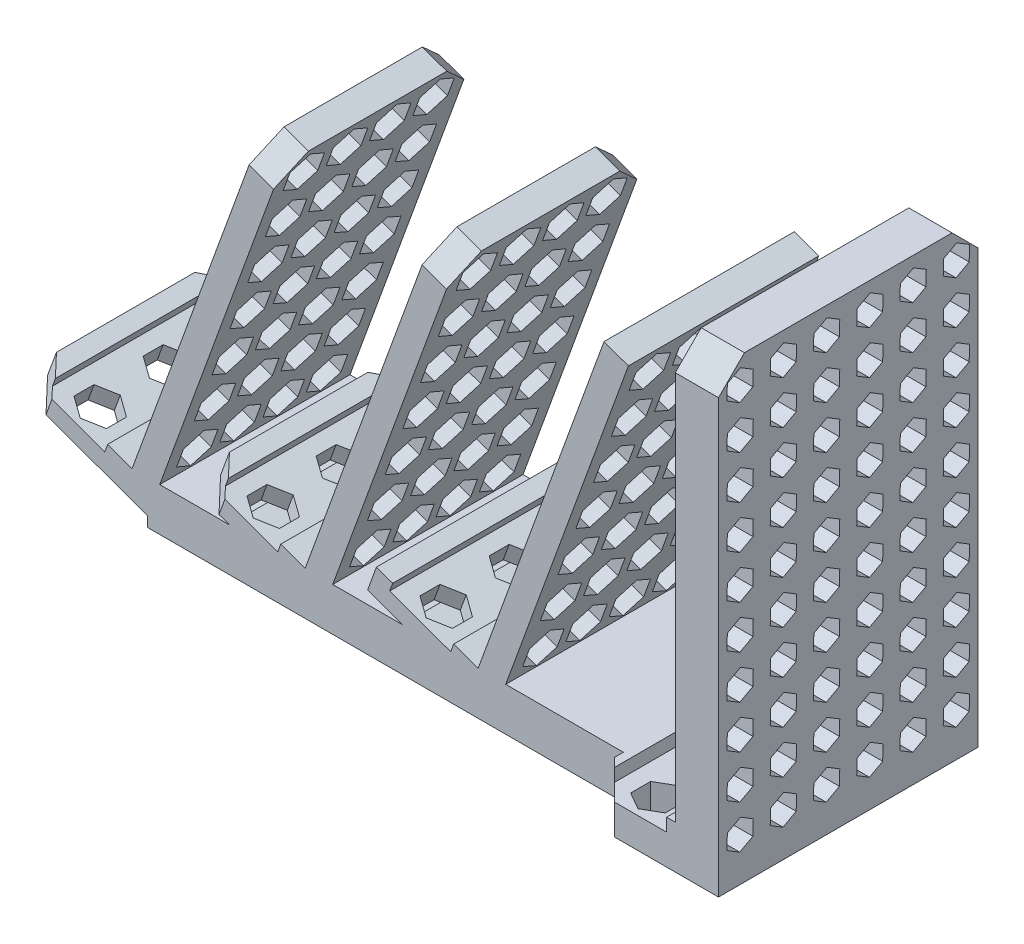
SolidWorks part; units mm, degrees
ref_plane "Front Plane" through (0, 0, 0) normal (0, 0, 1) x (1, 0, 0)
ref_plane "Top Plane" through (0, 0, 0) normal (0, 1, 0) x (1, 0, 0)
ref_plane "Right Plane" through (0, 0, 0) normal (1, 0, 0) x (0, 0, -1)
sketch "Sketch1" plane through (0, 0, 0) normal (0, 1, 0) x (1, 0, 0)
  line L1 (70, -22) -> (-70, -22)
  line L2 (70, -22) -> (70, 22)
  line L3 (70, 22) -> (-70, 22)
  line L4 (-70, -22) -> (-70, 22)
  line L5 (70, -22) -> (-70, 22) construction
  line L6 (70, 22) -> (-70, -22) construction
  point P0 (0, 0)
  dimension "D1" = 44
  dimension "D2" = 140
extrude "Boss-Extrude1" add sketch "Sketch1" along normal mid plane 10
sketch "Sketch2" plane through (0, 0, 0) normal (0, 0, 1) x (1, 0, 0)
  line L0 (-44.4684, 85) -> (-73.586, 5)
  line L1 (-70, -5) -> (70, -5) construction
  line L2 (-73.586, 5) -> (-97.0784, 13.5505)
  line L3 (-70, 5) -> (70, 5) construction
  line L4 (-38.8303, 82.9479) -> (-70, -2.6903)
  line L5 (-70, -2.6903) -> (-99.1305, 7.9123)
  line L6 (-99.1305, 7.9123) -> (-97.0784, 13.5505)
  line L7 (-44.4684, 85) -> (-38.8303, 82.9479)
  line L8 (-70, 5) -> (-70, -5) construction
  dimension "D1" = 20
  dimension "D2" = 25
  dimension "D3" = 80
  dimension "D4" = 6
  dimension "D5" = 0
extrude "Boss-Extrude2" add sketch "Sketch2" along normal mid plane 44
pattern_linear "LPattern1" count 3 spacing 40 along (1, 0, 0) of "Boss-Extrude2"
sketch "Sketch3" plane through (0, 5, 0) normal (0, 1, 0) x (1, 0, 0)
  line L5 (70, -22) -> (70, 22) construction
  line L6 (60, 30) -> (70, 30)
  line L7 (60, 30) -> (60, -30)
  line L8 (60, -30) -> (70, -30)
  line L9 (70, 30) -> (70, -30)
  line L10 (0, 0) -> (93.7204, 0) construction
  dimension "D1" = 30
  dimension "D2" = 60
  dimension "D3" = 10
extrude "Boss-Extrude3" add sketch "Sketch3" along normal blind 96 contours L9 L8 L7 L6
sketch "Sketch4" plane through (70, 0, 0) normal (1, 0, 0) x (0, 0, -1)
  line L0 (-22, -5) -> (22, -5) construction
  line L1 (-30, 5) -> (30, 5)
  line L2 (-30, 5) -> (-30, -5)
  line L3 (-30, -5) -> (30, -5)
  line L4 (30, 5) -> (30, -5)
  line L5 (30, 101) -> (30, 5) construction
extrude "Boss-Extrude4" add sketch "Sketch4" against normal blind 30
sketch "Sketch5" plane through (0, 0, 22) normal (0, 0, 1) x (1, 0, 0)
  line L0 (-93.3196, 12.1824) -> (-79.2242, 7.0521)
  line L1 (-73.586, 5) -> (-97.0784, 13.5505) construction
  line L2 (-79.2242, 7.0521) -> (-79.9082, 5.1727)
  line L3 (-79.9082, 5.1727) -> (-94.0036, 10.303)
  line L4 (-94.0036, 10.303) -> (-93.3196, 12.1824)
  line L5 (-44.4684, 85) -> (-73.586, 5) construction
  line L6 (-39.9082, 5.1727) -> (-54.0036, 10.303)
  line L7 (-53.3196, 12.1824) -> (-39.2242, 7.0521)
  line L8 (-54.0036, 10.303) -> (-53.3196, 12.1824)
  line L9 (-39.2242, 7.0521) -> (-39.9082, 5.1727)
  line L10 (0.0918, 5.1727) -> (-14.0036, 10.303)
  line L11 (-13.3196, 12.1824) -> (0.7758, 7.0521)
  line L12 (-14.0036, 10.303) -> (-13.3196, 12.1824)
  line L13 (0.7758, 7.0521) -> (0.0918, 5.1727)
  dimension "D1" = 90
  dimension "D2" = 2
  dimension "D3" = 15
  dimension "D4" = 6
  dimension "D5" = 3
extrude "Cut-Extrude1" cut sketch "Sketch5" against normal through all
sketch "Sketch6" plane through (0, 0, 30) normal (0, 0, 1) x (1, 0, 0)
  line L0 (40, 5) -> (60, 5) construction
  line L1 (42, 5) -> (58, 5)
  line L2 (42, 5) -> (42, 2)
  line L3 (42, 2) -> (58, 2)
  line L4 (58, 5) -> (58, 2)
  line L5 (40, 5) -> (40, -5) construction
  line L6 (60, 101) -> (60, 5) construction
  dimension "D1" = 2
  dimension "D2" = 2
  dimension "D3" = 3
extrude "Cut-Extrude2" cut sketch "Sketch6" against normal through all
sketch "Sketch7" plane through (-66.5851, 24.235, 0) normal (-0.9397, 0.342, 0) x (0, 0, 1)
  line L0 (-15, 64.6648) -> (-15, -20.4694) construction
  line L3 (22, 64.6648) -> (-22, 64.6648) construction
  line L10 (22, -20.4694) -> (-22, -20.4694) construction
  line L11 (-22, 64.6648) -> (-22, -20.4694) construction
  line L12 (-15, 63.2836) -> (-19, 60.9742)
  line L13 (-19, 60.9742) -> (-19, 56.3554)
  line L14 (-19, 56.3554) -> (-15, 54.046)
  line L15 (-15, 54.046) -> (-11, 56.3554)
  line L16 (-11, 56.3554) -> (-11, 60.9742)
  line L17 (-11, 60.9742) -> (-15, 63.2836)
  line L18 (-15, 51.2836) -> (-19, 48.9742)
  line L19 (-19, 44.3554) -> (-15, 42.046)
  line L20 (-19, 48.9742) -> (-19, 44.3554)
  line L21 (-11, 48.9742) -> (-15, 51.2836)
  line L22 (-11, 44.3554) -> (-11, 48.9742)
  line L23 (-15, 42.046) -> (-11, 44.3554)
  line L24 (-15, 39.2836) -> (-19, 36.9742)
  line L25 (-19, 32.3554) -> (-15, 30.046)
  line L26 (-19, 36.9742) -> (-19, 32.3554)
  line L27 (-11, 36.9742) -> (-15, 39.2836)
  line L28 (-11, 32.3554) -> (-11, 36.9742)
  line L29 (-15, 30.046) -> (-11, 32.3554)
  line L30 (-15, 27.2836) -> (-19, 24.9742)
  line L31 (-19, 20.3554) -> (-15, 18.046)
  line L32 (-19, 24.9742) -> (-19, 20.3554)
  line L33 (-11, 24.9742) -> (-15, 27.2836)
  line L34 (-11, 20.3554) -> (-11, 24.9742)
  line L35 (-15, 18.046) -> (-11, 20.3554)
  line L36 (-15, 15.2836) -> (-19, 12.9742)
  line L37 (-19, 8.3554) -> (-15, 6.046)
  line L38 (-19, 12.9742) -> (-19, 8.3554)
  line L39 (-11, 12.9742) -> (-15, 15.2836)
  line L40 (-11, 8.3554) -> (-11, 12.9742)
  line L41 (-15, 6.046) -> (-11, 8.3554)
  line L42 (-15, 3.2836) -> (-19, 0.9742)
  line L43 (-19, -3.6446) -> (-15, -5.954)
  line L44 (-19, 0.9742) -> (-19, -3.6446)
  line L45 (-11, 0.9742) -> (-15, 3.2836)
  line L46 (-11, -3.6446) -> (-11, 0.9742)
  line L47 (-15, -5.954) -> (-11, -3.6446)
  line L48 (-15, -8.7164) -> (-19, -11.0258)
  line L49 (-19, -15.6446) -> (-15, -17.954)
  line L50 (-19, -11.0258) -> (-19, -15.6446)
  line L51 (-11, -11.0258) -> (-15, -8.7164)
  line L52 (-11, -15.6446) -> (-11, -11.0258)
  line L53 (-15, -17.954) -> (-11, -15.6446)
  line L54 (-5, 51.2836) -> (-9, 48.9742)
  line L55 (-9, 44.3554) -> (-5, 42.046)
  line L56 (-9, 48.9742) -> (-9, 44.3554)
  line L57 (-1, 48.9742) -> (-5, 51.2836)
  line L58 (-1, 44.3554) -> (-1, 48.9742)
  line L59 (-5, 42.046) -> (-1, 44.3554)
  line L60 (-5, 39.2836) -> (-9, 36.9742)
  line L61 (-9, 32.3554) -> (-5, 30.046)
  line L62 (-9, 36.9742) -> (-9, 32.3554)
  line L63 (-1, 36.9742) -> (-5, 39.2836)
  line L64 (-1, 32.3554) -> (-1, 36.9742)
  line L65 (-5, 30.046) -> (-1, 32.3554)
  line L66 (-5, 27.2836) -> (-9, 24.9742)
  line L67 (-9, 20.3554) -> (-5, 18.046)
  line L68 (-9, 24.9742) -> (-9, 20.3554)
  line L69 (-1, 24.9742) -> (-5, 27.2836)
  line L70 (-1, 20.3554) -> (-1, 24.9742)
  line L71 (-5, 18.046) -> (-1, 20.3554)
  line L72 (-5, 15.2836) -> (-9, 12.9742)
  line L73 (-9, 8.3554) -> (-5, 6.046)
  line L74 (-9, 12.9742) -> (-9, 8.3554)
  line L75 (-1, 12.9742) -> (-5, 15.2836)
  line L76 (-1, 8.3554) -> (-1, 12.9742)
  line L77 (-5, 6.046) -> (-1, 8.3554)
  line L78 (-5, 3.2836) -> (-9, 0.9742)
  line L79 (-9, -3.6446) -> (-5, -5.954)
  line L80 (-9, 0.9742) -> (-9, -3.6446)
  line L81 (-1, 0.9742) -> (-5, 3.2836)
  line L82 (-1, -3.6446) -> (-1, 0.9742)
  line L83 (-5, -5.954) -> (-1, -3.6446)
  line L84 (-5, -8.7164) -> (-9, -11.0258)
  line L85 (-9, -15.6446) -> (-5, -17.954)
  line L86 (-9, -11.0258) -> (-9, -15.6446)
  line L87 (-1, -11.0258) -> (-5, -8.7164)
  line L88 (-1, -15.6446) -> (-1, -11.0258)
  line L89 (-5, -17.954) -> (-1, -15.6446)
  line L90 (5, 51.2836) -> (1, 48.9742)
  line L91 (1, 44.3554) -> (5, 42.046)
  line L92 (1, 48.9742) -> (1, 44.3554)
  line L93 (9, 48.9742) -> (5, 51.2836)
  line L94 (9, 44.3554) -> (9, 48.9742)
  line L95 (5, 42.046) -> (9, 44.3554)
  line L96 (5, 39.2836) -> (1, 36.9742)
  line L97 (1, 32.3554) -> (5, 30.046)
  line L98 (1, 36.9742) -> (1, 32.3554)
  line L99 (9, 36.9742) -> (5, 39.2836)
  line L100 (9, 32.3554) -> (9, 36.9742)
  line L101 (5, 30.046) -> (9, 32.3554)
  line L102 (5, 27.2836) -> (1, 24.9742)
  line L103 (1, 20.3554) -> (5, 18.046)
  line L104 (1, 24.9742) -> (1, 20.3554)
  line L105 (9, 24.9742) -> (5, 27.2836)
  line L106 (9, 20.3554) -> (9, 24.9742)
  line L107 (5, 18.046) -> (9, 20.3554)
  line L108 (5, 15.2836) -> (1, 12.9742)
  line L109 (1, 8.3554) -> (5, 6.046)
  line L110 (1, 12.9742) -> (1, 8.3554)
  line L111 (9, 12.9742) -> (5, 15.2836)
  line L112 (9, 8.3554) -> (9, 12.9742)
  line L113 (5, 6.046) -> (9, 8.3554)
  line L114 (5, 3.2836) -> (1, 0.9742)
  line L115 (1, -3.6446) -> (5, -5.954)
  line L116 (1, 0.9742) -> (1, -3.6446)
  line L117 (9, 0.9742) -> (5, 3.2836)
  line L118 (9, -3.6446) -> (9, 0.9742)
  line L119 (5, -5.954) -> (9, -3.6446)
  line L120 (5, -8.7164) -> (1, -11.0258)
  line L121 (1, -15.6446) -> (5, -17.954)
  line L122 (1, -11.0258) -> (1, -15.6446)
  line L123 (9, -11.0258) -> (5, -8.7164)
  line L124 (9, -15.6446) -> (9, -11.0258)
  line L125 (5, -17.954) -> (9, -15.6446)
  line L126 (15, 51.2836) -> (11, 48.9742)
  line L127 (11, 44.3554) -> (15, 42.046)
  line L128 (11, 48.9742) -> (11, 44.3554)
  line L129 (19, 48.9742) -> (15, 51.2836)
  line L130 (19, 44.3554) -> (19, 48.9742)
  line L131 (15, 42.046) -> (19, 44.3554)
  line L132 (15, 39.2836) -> (11, 36.9742)
  line L133 (11, 32.3554) -> (15, 30.046)
  line L134 (11, 36.9742) -> (11, 32.3554)
  line L135 (19, 36.9742) -> (15, 39.2836)
  line L136 (19, 32.3554) -> (19, 36.9742)
  line L137 (15, 30.046) -> (19, 32.3554)
  line L138 (15, 27.2836) -> (11, 24.9742)
  line L139 (11, 20.3554) -> (15, 18.046)
  line L140 (11, 24.9742) -> (11, 20.3554)
  line L141 (19, 24.9742) -> (15, 27.2836)
  line L142 (19, 20.3554) -> (19, 24.9742)
  line L143 (15, 18.046) -> (19, 20.3554)
  line L144 (15, 15.2836) -> (11, 12.9742)
  line L145 (11, 8.3554) -> (15, 6.046)
  line L146 (11, 12.9742) -> (11, 8.3554)
  line L147 (19, 12.9742) -> (15, 15.2836)
  line L148 (19, 8.3554) -> (19, 12.9742)
  line L149 (15, 6.046) -> (19, 8.3554)
  line L150 (15, 3.2836) -> (11, 0.9742)
  line L151 (11, -3.6446) -> (15, -5.954)
  line L152 (11, 0.9742) -> (11, -3.6446)
  line L153 (19, 0.9742) -> (15, 3.2836)
  line L154 (19, -3.6446) -> (19, 0.9742)
  line L155 (15, -5.954) -> (19, -3.6446)
  line L156 (15, -8.7164) -> (11, -11.0258)
  line L157 (11, -15.6446) -> (15, -17.954)
  line L158 (11, -11.0258) -> (11, -15.6446)
  line L159 (19, -11.0258) -> (15, -8.7164)
  line L160 (19, -15.6446) -> (19, -11.0258)
  line L161 (15, -17.954) -> (19, -15.6446)
  line L162 (-5, 63.2836) -> (-9, 60.9742)
  line L163 (-9, 56.3554) -> (-5, 54.046)
  line L164 (-9, 60.9742) -> (-9, 56.3554)
  line L165 (-1, 60.9742) -> (-5, 63.2836)
  line L166 (-1, 56.3554) -> (-1, 60.9742)
  line L167 (-5, 54.046) -> (-1, 56.3554)
  line L168 (5, 63.2836) -> (1, 60.9742)
  line L169 (1, 56.3554) -> (5, 54.046)
  line L170 (1, 60.9742) -> (1, 56.3554)
  line L171 (9, 60.9742) -> (5, 63.2836)
  line L172 (9, 56.3554) -> (9, 60.9742)
  line L173 (5, 54.046) -> (9, 56.3554)
  line L174 (15, 63.2836) -> (11, 60.9742)
  line L175 (11, 56.3554) -> (15, 54.046)
  line L176 (11, 60.9742) -> (11, 56.3554)
  line L177 (19, 60.9742) -> (15, 63.2836)
  line L178 (19, 56.3554) -> (19, 60.9742)
  line L179 (15, 54.046) -> (19, 56.3554)
  circle A0 centre (-15, 58.6648) radius 4 construction
  circle A1 centre (-15, 46.6648) radius 4 construction
  circle A2 centre (-15, 34.6648) radius 4 construction
  circle A3 centre (-15, 22.6648) radius 4 construction
  circle A4 centre (-15, 10.6648) radius 4 construction
  circle A5 centre (-15, -1.3352) radius 4 construction
  circle A6 centre (-15, -13.3352) radius 4 construction
  circle A7 centre (-5, 46.6648) radius 4 construction
  circle A8 centre (-5, 34.6648) radius 4 construction
  circle A9 centre (-5, 22.6648) radius 4 construction
  circle A10 centre (-5, 10.6648) radius 4 construction
  circle A11 centre (-5, -1.3352) radius 4 construction
  circle A12 centre (-5, -13.3352) radius 4 construction
  circle A13 centre (5, 46.6648) radius 4 construction
  circle A14 centre (5, 34.6648) radius 4 construction
  circle A15 centre (5, 22.6648) radius 4 construction
  circle A16 centre (5, 10.6648) radius 4 construction
  circle A17 centre (5, -1.3352) radius 4 construction
  circle A18 centre (5, -13.3352) radius 4 construction
  circle A19 centre (15, 46.6648) radius 4 construction
  circle A20 centre (15, 34.6648) radius 4 construction
  circle A21 centre (15, 22.6648) radius 4 construction
  circle A22 centre (15, 10.6648) radius 4 construction
  circle A23 centre (15, -1.3352) radius 4 construction
  circle A24 centre (15, -13.3352) radius 4 construction
  circle A25 centre (-5, 58.6648) radius 4 construction
  circle A26 centre (5, 58.6648) radius 4 construction
  circle A27 centre (15, 58.6648) radius 4 construction
  dimension "D2" = 6
  dimension "D1" = 8
  dimension "D3" = 7
  dimension "D4" = 7
  dimension "D5" = 4
extrude "Cut-Extrude3" cut sketch "Sketch7" against normal up to surface (6 mm away) up to face at (-53.0156, 43.9739, 0)
pattern_linear "LPattern2" count 3 spacing 40 along (0.342, 0.9397, 0) of "Cut-Extrude3"
sketch "Sketch12" plane through (70, 0, 0) normal (1, 0, 0) x (0, 0, -1)
  line L0 (-30, 101) -> (-30, -5) construction
  line L1 (-22.041, 93.1989) -> (-21.9606, 96.662)
  line L2 (-21.9606, 96.662) -> (-24.9197, 98.4632)
  line L3 (-24.9197, 98.4632) -> (-27.959, 96.8011)
  line L4 (-27.959, 96.8011) -> (-28.0394, 93.338)
  line L5 (-28.0394, 93.338) -> (-25.0803, 91.5368)
  line L6 (-25.0803, 91.5368) -> (-22.041, 93.1989)
  line L7 (30, 101) -> (-30, 101) construction
  line L8 (-24.9197, 88.4632) -> (-27.959, 86.8011)
  line L9 (-21.9606, 86.662) -> (-24.9197, 88.4632)
  line L10 (-22.041, 83.1989) -> (-21.9606, 86.662)
  line L11 (-25.0803, 81.5368) -> (-22.041, 83.1989)
  line L12 (-28.0394, 83.338) -> (-25.0803, 81.5368)
  line L13 (-27.959, 86.8011) -> (-28.0394, 83.338)
  line L14 (-24.9197, 78.4632) -> (-27.959, 76.8011)
  line L15 (-21.9606, 76.662) -> (-24.9197, 78.4632)
  line L16 (-22.041, 73.1989) -> (-21.9606, 76.662)
  line L17 (-25.0803, 71.5368) -> (-22.041, 73.1989)
  line L18 (-28.0394, 73.338) -> (-25.0803, 71.5368)
  line L19 (-27.959, 76.8011) -> (-28.0394, 73.338)
  line L20 (-24.9197, 68.4632) -> (-27.959, 66.8011)
  line L21 (-21.9606, 66.662) -> (-24.9197, 68.4632)
  line L22 (-22.041, 63.1989) -> (-21.9606, 66.662)
  line L23 (-25.0803, 61.5368) -> (-22.041, 63.1989)
  line L24 (-28.0394, 63.338) -> (-25.0803, 61.5368)
  line L25 (-27.959, 66.8011) -> (-28.0394, 63.338)
  line L26 (-24.9197, 58.4632) -> (-27.959, 56.8011)
  line L27 (-21.9606, 56.662) -> (-24.9197, 58.4632)
  line L28 (-22.041, 53.1989) -> (-21.9606, 56.662)
  line L29 (-25.0803, 51.5368) -> (-22.041, 53.1989)
  line L30 (-28.0394, 53.338) -> (-25.0803, 51.5368)
  line L31 (-27.959, 56.8011) -> (-28.0394, 53.338)
  line L32 (-24.9197, 48.4632) -> (-27.959, 46.8011)
  line L33 (-21.9606, 46.662) -> (-24.9197, 48.4632)
  line L34 (-22.041, 43.1989) -> (-21.9606, 46.662)
  line L35 (-25.0803, 41.5368) -> (-22.041, 43.1989)
  line L36 (-28.0394, 43.338) -> (-25.0803, 41.5368)
  line L37 (-27.959, 46.8011) -> (-28.0394, 43.338)
  line L38 (-24.9197, 38.4632) -> (-27.959, 36.8011)
  line L39 (-21.9606, 36.662) -> (-24.9197, 38.4632)
  line L40 (-22.041, 33.1989) -> (-21.9606, 36.662)
  line L41 (-25.0803, 31.5368) -> (-22.041, 33.1989)
  line L42 (-28.0394, 33.338) -> (-25.0803, 31.5368)
  line L43 (-27.959, 36.8011) -> (-28.0394, 33.338)
  line L44 (-24.9197, 28.4632) -> (-27.959, 26.8011)
  line L45 (-21.9606, 26.662) -> (-24.9197, 28.4632)
  line L46 (-22.041, 23.1989) -> (-21.9606, 26.662)
  line L47 (-25.0803, 21.5368) -> (-22.041, 23.1989)
  line L48 (-28.0394, 23.338) -> (-25.0803, 21.5368)
  line L49 (-27.959, 26.8011) -> (-28.0394, 23.338)
  line L50 (-24.9197, 18.4632) -> (-27.959, 16.8011)
  line L51 (-21.9606, 16.662) -> (-24.9197, 18.4632)
  line L52 (-22.041, 13.1989) -> (-21.9606, 16.662)
  line L53 (-25.0803, 11.5368) -> (-22.041, 13.1989)
  line L54 (-28.0394, 13.338) -> (-25.0803, 11.5368)
  line L55 (-27.959, 16.8011) -> (-28.0394, 13.338)
  line L56 (-24.9197, 8.4632) -> (-27.959, 6.8011)
  line L57 (-21.9606, 6.662) -> (-24.9197, 8.4632)
  line L58 (-22.041, 3.1989) -> (-21.9606, 6.662)
  line L59 (-25.0803, 1.5368) -> (-22.041, 3.1989)
  line L60 (-28.0394, 3.338) -> (-25.0803, 1.5368)
  line L61 (-27.959, 6.8011) -> (-28.0394, 3.338)
  line L62 (-14.9197, 88.4632) -> (-17.959, 86.8011)
  line L63 (-11.9606, 86.662) -> (-14.9197, 88.4632)
  line L64 (-12.041, 83.1989) -> (-11.9606, 86.662)
  line L65 (-15.0803, 81.5368) -> (-12.041, 83.1989)
  line L66 (-18.0394, 83.338) -> (-15.0803, 81.5368)
  line L67 (-17.959, 86.8011) -> (-18.0394, 83.338)
  line L68 (-14.9197, 78.4632) -> (-17.959, 76.8011)
  line L69 (-11.9606, 76.662) -> (-14.9197, 78.4632)
  line L70 (-12.041, 73.1989) -> (-11.9606, 76.662)
  line L71 (-15.0803, 71.5368) -> (-12.041, 73.1989)
  line L72 (-18.0394, 73.338) -> (-15.0803, 71.5368)
  line L73 (-17.959, 76.8011) -> (-18.0394, 73.338)
  line L74 (-14.9197, 68.4632) -> (-17.959, 66.8011)
  line L75 (-11.9606, 66.662) -> (-14.9197, 68.4632)
  line L76 (-12.041, 63.1989) -> (-11.9606, 66.662)
  line L77 (-15.0803, 61.5368) -> (-12.041, 63.1989)
  line L78 (-18.0394, 63.338) -> (-15.0803, 61.5368)
  line L79 (-17.959, 66.8011) -> (-18.0394, 63.338)
  line L80 (-14.9197, 58.4632) -> (-17.959, 56.8011)
  line L81 (-11.9606, 56.662) -> (-14.9197, 58.4632)
  line L82 (-12.041, 53.1989) -> (-11.9606, 56.662)
  line L83 (-15.0803, 51.5368) -> (-12.041, 53.1989)
  line L84 (-18.0394, 53.338) -> (-15.0803, 51.5368)
  line L85 (-17.959, 56.8011) -> (-18.0394, 53.338)
  line L86 (-14.9197, 48.4632) -> (-17.959, 46.8011)
  line L87 (-11.9606, 46.662) -> (-14.9197, 48.4632)
  line L88 (-12.041, 43.1989) -> (-11.9606, 46.662)
  line L89 (-15.0803, 41.5368) -> (-12.041, 43.1989)
  line L90 (-18.0394, 43.338) -> (-15.0803, 41.5368)
  line L91 (-17.959, 46.8011) -> (-18.0394, 43.338)
  line L92 (-14.9197, 38.4632) -> (-17.959, 36.8011)
  line L93 (-11.9606, 36.662) -> (-14.9197, 38.4632)
  line L94 (-12.041, 33.1989) -> (-11.9606, 36.662)
  line L95 (-15.0803, 31.5368) -> (-12.041, 33.1989)
  line L96 (-18.0394, 33.338) -> (-15.0803, 31.5368)
  line L97 (-17.959, 36.8011) -> (-18.0394, 33.338)
  line L98 (-14.9197, 28.4632) -> (-17.959, 26.8011)
  line L99 (-11.9606, 26.662) -> (-14.9197, 28.4632)
  line L100 (-12.041, 23.1989) -> (-11.9606, 26.662)
  line L101 (-15.0803, 21.5368) -> (-12.041, 23.1989)
  line L102 (-18.0394, 23.338) -> (-15.0803, 21.5368)
  line L103 (-17.959, 26.8011) -> (-18.0394, 23.338)
  line L104 (-14.9197, 18.4632) -> (-17.959, 16.8011)
  line L105 (-11.9606, 16.662) -> (-14.9197, 18.4632)
  line L106 (-12.041, 13.1989) -> (-11.9606, 16.662)
  line L107 (-15.0803, 11.5368) -> (-12.041, 13.1989)
  line L108 (-18.0394, 13.338) -> (-15.0803, 11.5368)
  line L109 (-17.959, 16.8011) -> (-18.0394, 13.338)
  line L110 (-14.9197, 8.4632) -> (-17.959, 6.8011)
  line L111 (-11.9606, 6.662) -> (-14.9197, 8.4632)
  line L112 (-12.041, 3.1989) -> (-11.9606, 6.662)
  line L113 (-15.0803, 1.5368) -> (-12.041, 3.1989)
  line L114 (-18.0394, 3.338) -> (-15.0803, 1.5368)
  line L115 (-17.959, 6.8011) -> (-18.0394, 3.338)
  line L116 (-4.9197, 88.4632) -> (-7.959, 86.8011)
  line L117 (-1.9606, 86.662) -> (-4.9197, 88.4632)
  line L118 (-2.041, 83.1989) -> (-1.9606, 86.662)
  line L119 (-5.0803, 81.5368) -> (-2.041, 83.1989)
  line L120 (-8.0394, 83.338) -> (-5.0803, 81.5368)
  line L121 (-7.959, 86.8011) -> (-8.0394, 83.338)
  line L122 (-4.9197, 78.4632) -> (-7.959, 76.8011)
  line L123 (-1.9606, 76.662) -> (-4.9197, 78.4632)
  line L124 (-2.041, 73.1989) -> (-1.9606, 76.662)
  line L125 (-5.0803, 71.5368) -> (-2.041, 73.1989)
  line L126 (-8.0394, 73.338) -> (-5.0803, 71.5368)
  line L127 (-7.959, 76.8011) -> (-8.0394, 73.338)
  line L128 (-4.9197, 68.4632) -> (-7.959, 66.8011)
  line L129 (-1.9606, 66.662) -> (-4.9197, 68.4632)
  line L130 (-2.041, 63.1989) -> (-1.9606, 66.662)
  line L131 (-5.0803, 61.5368) -> (-2.041, 63.1989)
  line L132 (-8.0394, 63.338) -> (-5.0803, 61.5368)
  line L133 (-7.959, 66.8011) -> (-8.0394, 63.338)
  line L134 (-4.9197, 58.4632) -> (-7.959, 56.8011)
  line L135 (-1.9606, 56.662) -> (-4.9197, 58.4632)
  line L136 (-2.041, 53.1989) -> (-1.9606, 56.662)
  line L137 (-5.0803, 51.5368) -> (-2.041, 53.1989)
  line L138 (-8.0394, 53.338) -> (-5.0803, 51.5368)
  line L139 (-7.959, 56.8011) -> (-8.0394, 53.338)
  line L140 (-4.9197, 48.4632) -> (-7.959, 46.8011)
  line L141 (-1.9606, 46.662) -> (-4.9197, 48.4632)
  line L142 (-2.041, 43.1989) -> (-1.9606, 46.662)
  line L143 (-5.0803, 41.5368) -> (-2.041, 43.1989)
  line L144 (-8.0394, 43.338) -> (-5.0803, 41.5368)
  line L145 (-7.959, 46.8011) -> (-8.0394, 43.338)
  line L146 (-4.9197, 38.4632) -> (-7.959, 36.8011)
  line L147 (-1.9606, 36.662) -> (-4.9197, 38.4632)
  line L148 (-2.041, 33.1989) -> (-1.9606, 36.662)
  line L149 (-5.0803, 31.5368) -> (-2.041, 33.1989)
  line L150 (-8.0394, 33.338) -> (-5.0803, 31.5368)
  line L151 (-7.959, 36.8011) -> (-8.0394, 33.338)
  line L152 (-4.9197, 28.4632) -> (-7.959, 26.8011)
  line L153 (-1.9606, 26.662) -> (-4.9197, 28.4632)
  line L154 (-2.041, 23.1989) -> (-1.9606, 26.662)
  line L155 (-5.0803, 21.5368) -> (-2.041, 23.1989)
  line L156 (-8.0394, 23.338) -> (-5.0803, 21.5368)
  line L157 (-7.959, 26.8011) -> (-8.0394, 23.338)
  line L158 (-4.9197, 18.4632) -> (-7.959, 16.8011)
  line L159 (-1.9606, 16.662) -> (-4.9197, 18.4632)
  line L160 (-2.041, 13.1989) -> (-1.9606, 16.662)
  line L161 (-5.0803, 11.5368) -> (-2.041, 13.1989)
  line L162 (-8.0394, 13.338) -> (-5.0803, 11.5368)
  line L163 (-7.959, 16.8011) -> (-8.0394, 13.338)
  line L164 (-4.9197, 8.4632) -> (-7.959, 6.8011)
  line L165 (-1.9606, 6.662) -> (-4.9197, 8.4632)
  line L166 (-2.041, 3.1989) -> (-1.9606, 6.662)
  line L167 (-5.0803, 1.5368) -> (-2.041, 3.1989)
  line L168 (-8.0394, 3.338) -> (-5.0803, 1.5368)
  line L169 (-7.959, 6.8011) -> (-8.0394, 3.338)
  line L170 (5.0803, 88.4632) -> (2.041, 86.8011)
  line L171 (8.0394, 86.662) -> (5.0803, 88.4632)
  line L172 (7.959, 83.1989) -> (8.0394, 86.662)
  line L173 (4.9197, 81.5368) -> (7.959, 83.1989)
  line L174 (1.9606, 83.338) -> (4.9197, 81.5368)
  line L175 (2.041, 86.8011) -> (1.9606, 83.338)
  line L176 (5.0803, 78.4632) -> (2.041, 76.8011)
  line L177 (8.0394, 76.662) -> (5.0803, 78.4632)
  line L178 (7.959, 73.1989) -> (8.0394, 76.662)
  line L179 (4.9197, 71.5368) -> (7.959, 73.1989)
  line L180 (1.9606, 73.338) -> (4.9197, 71.5368)
  line L181 (2.041, 76.8011) -> (1.9606, 73.338)
  line L182 (5.0803, 68.4632) -> (2.041, 66.8011)
  line L183 (8.0394, 66.662) -> (5.0803, 68.4632)
  line L184 (7.959, 63.1989) -> (8.0394, 66.662)
  line L185 (4.9197, 61.5368) -> (7.959, 63.1989)
  line L186 (1.9606, 63.338) -> (4.9197, 61.5368)
  line L187 (2.041, 66.8011) -> (1.9606, 63.338)
  line L188 (5.0803, 58.4632) -> (2.041, 56.8011)
  line L189 (8.0394, 56.662) -> (5.0803, 58.4632)
  line L190 (7.959, 53.1989) -> (8.0394, 56.662)
  line L191 (4.9197, 51.5368) -> (7.959, 53.1989)
  line L192 (1.9606, 53.338) -> (4.9197, 51.5368)
  line L193 (2.041, 56.8011) -> (1.9606, 53.338)
  line L194 (5.0803, 48.4632) -> (2.041, 46.8011)
  line L195 (8.0394, 46.662) -> (5.0803, 48.4632)
  line L196 (7.959, 43.1989) -> (8.0394, 46.662)
  line L197 (4.9197, 41.5368) -> (7.959, 43.1989)
  line L198 (1.9606, 43.338) -> (4.9197, 41.5368)
  line L199 (2.041, 46.8011) -> (1.9606, 43.338)
  line L200 (5.0803, 38.4632) -> (2.041, 36.8011)
  line L201 (8.0394, 36.662) -> (5.0803, 38.4632)
  line L202 (7.959, 33.1989) -> (8.0394, 36.662)
  line L203 (4.9197, 31.5368) -> (7.959, 33.1989)
  line L204 (1.9606, 33.338) -> (4.9197, 31.5368)
  line L205 (2.041, 36.8011) -> (1.9606, 33.338)
  line L206 (5.0803, 28.4632) -> (2.041, 26.8011)
  line L207 (8.0394, 26.662) -> (5.0803, 28.4632)
  line L208 (7.959, 23.1989) -> (8.0394, 26.662)
  line L209 (4.9197, 21.5368) -> (7.959, 23.1989)
  line L210 (1.9606, 23.338) -> (4.9197, 21.5368)
  line L211 (2.041, 26.8011) -> (1.9606, 23.338)
  line L212 (5.0803, 18.4632) -> (2.041, 16.8011)
  line L213 (8.0394, 16.662) -> (5.0803, 18.4632)
  line L214 (7.959, 13.1989) -> (8.0394, 16.662)
  line L215 (4.9197, 11.5368) -> (7.959, 13.1989)
  line L216 (1.9606, 13.338) -> (4.9197, 11.5368)
  line L217 (2.041, 16.8011) -> (1.9606, 13.338)
  line L218 (5.0803, 8.4632) -> (2.041, 6.8011)
  line L219 (8.0394, 6.662) -> (5.0803, 8.4632)
  line L220 (7.959, 3.1989) -> (8.0394, 6.662)
  line L221 (4.9197, 1.5368) -> (7.959, 3.1989)
  line L222 (1.9606, 3.338) -> (4.9197, 1.5368)
  line L223 (2.041, 6.8011) -> (1.9606, 3.338)
  line L224 (15.0803, 88.4632) -> (12.041, 86.8011)
  line L225 (18.0394, 86.662) -> (15.0803, 88.4632)
  line L226 (17.959, 83.1989) -> (18.0394, 86.662)
  line L227 (14.9197, 81.5368) -> (17.959, 83.1989)
  line L228 (11.9606, 83.338) -> (14.9197, 81.5368)
  line L229 (12.041, 86.8011) -> (11.9606, 83.338)
  line L230 (15.0803, 78.4632) -> (12.041, 76.8011)
  line L231 (18.0394, 76.662) -> (15.0803, 78.4632)
  line L232 (17.959, 73.1989) -> (18.0394, 76.662)
  line L233 (14.9197, 71.5368) -> (17.959, 73.1989)
  line L234 (11.9606, 73.338) -> (14.9197, 71.5368)
  line L235 (12.041, 76.8011) -> (11.9606, 73.338)
  line L236 (15.0803, 68.4632) -> (12.041, 66.8011)
  line L237 (18.0394, 66.662) -> (15.0803, 68.4632)
  line L238 (17.959, 63.1989) -> (18.0394, 66.662)
  line L239 (14.9197, 61.5368) -> (17.959, 63.1989)
  line L240 (11.9606, 63.338) -> (14.9197, 61.5368)
  line L241 (12.041, 66.8011) -> (11.9606, 63.338)
  line L242 (15.0803, 58.4632) -> (12.041, 56.8011)
  line L243 (18.0394, 56.662) -> (15.0803, 58.4632)
  line L244 (17.959, 53.1989) -> (18.0394, 56.662)
  line L245 (14.9197, 51.5368) -> (17.959, 53.1989)
  line L246 (11.9606, 53.338) -> (14.9197, 51.5368)
  line L247 (12.041, 56.8011) -> (11.9606, 53.338)
  line L248 (15.0803, 48.4632) -> (12.041, 46.8011)
  line L249 (18.0394, 46.662) -> (15.0803, 48.4632)
  line L250 (17.959, 43.1989) -> (18.0394, 46.662)
  line L251 (14.9197, 41.5368) -> (17.959, 43.1989)
  line L252 (11.9606, 43.338) -> (14.9197, 41.5368)
  line L253 (12.041, 46.8011) -> (11.9606, 43.338)
  line L254 (15.0803, 38.4632) -> (12.041, 36.8011)
  line L255 (18.0394, 36.662) -> (15.0803, 38.4632)
  line L256 (17.959, 33.1989) -> (18.0394, 36.662)
  line L257 (14.9197, 31.5368) -> (17.959, 33.1989)
  line L258 (11.9606, 33.338) -> (14.9197, 31.5368)
  line L259 (12.041, 36.8011) -> (11.9606, 33.338)
  line L260 (15.0803, 28.4632) -> (12.041, 26.8011)
  line L261 (18.0394, 26.662) -> (15.0803, 28.4632)
  line L262 (17.959, 23.1989) -> (18.0394, 26.662)
  line L263 (14.9197, 21.5368) -> (17.959, 23.1989)
  line L264 (11.9606, 23.338) -> (14.9197, 21.5368)
  line L265 (12.041, 26.8011) -> (11.9606, 23.338)
  line L266 (15.0803, 18.4632) -> (12.041, 16.8011)
  line L267 (18.0394, 16.662) -> (15.0803, 18.4632)
  line L268 (17.959, 13.1989) -> (18.0394, 16.662)
  line L269 (14.9197, 11.5368) -> (17.959, 13.1989)
  line L270 (11.9606, 13.338) -> (14.9197, 11.5368)
  line L271 (12.041, 16.8011) -> (11.9606, 13.338)
  line L272 (15.0803, 8.4632) -> (12.041, 6.8011)
  line L273 (18.0394, 6.662) -> (15.0803, 8.4632)
  line L274 (17.959, 3.1989) -> (18.0394, 6.662)
  line L275 (14.9197, 1.5368) -> (17.959, 3.1989)
  line L276 (11.9606, 3.338) -> (14.9197, 1.5368)
  line L277 (12.041, 6.8011) -> (11.9606, 3.338)
  line L278 (25.0803, 88.4632) -> (22.041, 86.8011)
  line L279 (28.0394, 86.662) -> (25.0803, 88.4632)
  line L280 (27.959, 83.1989) -> (28.0394, 86.662)
  line L281 (24.9197, 81.5368) -> (27.959, 83.1989)
  line L282 (21.9606, 83.338) -> (24.9197, 81.5368)
  line L283 (22.041, 86.8011) -> (21.9606, 83.338)
  line L284 (25.0803, 78.4632) -> (22.041, 76.8011)
  line L285 (28.0394, 76.662) -> (25.0803, 78.4632)
  line L286 (27.959, 73.1989) -> (28.0394, 76.662)
  line L287 (24.9197, 71.5368) -> (27.959, 73.1989)
  line L288 (21.9606, 73.338) -> (24.9197, 71.5368)
  line L289 (22.041, 76.8011) -> (21.9606, 73.338)
  line L290 (25.0803, 68.4632) -> (22.041, 66.8011)
  line L291 (28.0394, 66.662) -> (25.0803, 68.4632)
  line L292 (27.959, 63.1989) -> (28.0394, 66.662)
  line L293 (24.9197, 61.5368) -> (27.959, 63.1989)
  line L294 (21.9606, 63.338) -> (24.9197, 61.5368)
  line L295 (22.041, 66.8011) -> (21.9606, 63.338)
  line L296 (25.0803, 58.4632) -> (22.041, 56.8011)
  line L297 (28.0394, 56.662) -> (25.0803, 58.4632)
  line L298 (27.959, 53.1989) -> (28.0394, 56.662)
  line L299 (24.9197, 51.5368) -> (27.959, 53.1989)
  line L300 (21.9606, 53.338) -> (24.9197, 51.5368)
  line L301 (22.041, 56.8011) -> (21.9606, 53.338)
  line L302 (25.0803, 48.4632) -> (22.041, 46.8011)
  line L303 (28.0394, 46.662) -> (25.0803, 48.4632)
  line L304 (27.959, 43.1989) -> (28.0394, 46.662)
  line L305 (24.9197, 41.5368) -> (27.959, 43.1989)
  line L306 (21.9606, 43.338) -> (24.9197, 41.5368)
  line L307 (22.041, 46.8011) -> (21.9606, 43.338)
  line L308 (25.0803, 38.4632) -> (22.041, 36.8011)
  line L309 (28.0394, 36.662) -> (25.0803, 38.4632)
  line L310 (27.959, 33.1989) -> (28.0394, 36.662)
  line L311 (24.9197, 31.5368) -> (27.959, 33.1989)
  line L312 (21.9606, 33.338) -> (24.9197, 31.5368)
  line L313 (22.041, 36.8011) -> (21.9606, 33.338)
  line L314 (25.0803, 28.4632) -> (22.041, 26.8011)
  line L315 (28.0394, 26.662) -> (25.0803, 28.4632)
  line L316 (27.959, 23.1989) -> (28.0394, 26.662)
  line L317 (24.9197, 21.5368) -> (27.959, 23.1989)
  line L318 (21.9606, 23.338) -> (24.9197, 21.5368)
  line L319 (22.041, 26.8011) -> (21.9606, 23.338)
  line L320 (25.0803, 18.4632) -> (22.041, 16.8011)
  line L321 (28.0394, 16.662) -> (25.0803, 18.4632)
  line L322 (27.959, 13.1989) -> (28.0394, 16.662)
  line L323 (24.9197, 11.5368) -> (27.959, 13.1989)
  line L324 (21.9606, 13.338) -> (24.9197, 11.5368)
  line L325 (22.041, 16.8011) -> (21.9606, 13.338)
  line L326 (25.0803, 8.4632) -> (22.041, 6.8011)
  line L327 (28.0394, 6.662) -> (25.0803, 8.4632)
  line L328 (27.959, 3.1989) -> (28.0394, 6.662)
  line L329 (24.9197, 1.5368) -> (27.959, 3.1989)
  line L330 (21.9606, 3.338) -> (24.9197, 1.5368)
  line L331 (22.041, 6.8011) -> (21.9606, 3.338)
  line L332 (-14.9197, 98.4632) -> (-17.959, 96.8011)
  line L333 (-11.9606, 96.662) -> (-14.9197, 98.4632)
  line L334 (-12.041, 93.1989) -> (-11.9606, 96.662)
  line L335 (-15.0803, 91.5368) -> (-12.041, 93.1989)
  line L336 (-18.0394, 93.338) -> (-15.0803, 91.5368)
  line L337 (-17.959, 96.8011) -> (-18.0394, 93.338)
  line L338 (-4.9197, 98.4632) -> (-7.959, 96.8011)
  line L339 (-1.9606, 96.662) -> (-4.9197, 98.4632)
  line L340 (-2.041, 93.1989) -> (-1.9606, 96.662)
  line L341 (-5.0803, 91.5368) -> (-2.041, 93.1989)
  line L342 (-8.0394, 93.338) -> (-5.0803, 91.5368)
  line L343 (-7.959, 96.8011) -> (-8.0394, 93.338)
  line L344 (5.0803, 98.4632) -> (2.041, 96.8011)
  line L345 (8.0394, 96.662) -> (5.0803, 98.4632)
  line L346 (7.959, 93.1989) -> (8.0394, 96.662)
  line L347 (4.9197, 91.5368) -> (7.959, 93.1989)
  line L348 (1.9606, 93.338) -> (4.9197, 91.5368)
  line L349 (2.041, 96.8011) -> (1.9606, 93.338)
  line L350 (15.0803, 98.4632) -> (12.041, 96.8011)
  line L351 (18.0394, 96.662) -> (15.0803, 98.4632)
  line L352 (17.959, 93.1989) -> (18.0394, 96.662)
  line L353 (14.9197, 91.5368) -> (17.959, 93.1989)
  line L354 (11.9606, 93.338) -> (14.9197, 91.5368)
  line L355 (12.041, 96.8011) -> (11.9606, 93.338)
  line L356 (25.0803, 98.4632) -> (22.041, 96.8011)
  line L357 (28.0394, 96.662) -> (25.0803, 98.4632)
  line L358 (27.959, 93.1989) -> (28.0394, 96.662)
  line L359 (24.9197, 91.5368) -> (27.959, 93.1989)
  line L360 (21.9606, 93.338) -> (24.9197, 91.5368)
  line L361 (22.041, 96.8011) -> (21.9606, 93.338)
  circle A0 centre (-25, 95) radius 3 construction
  circle A1 centre (-25, 85) radius 3 construction
  circle A2 centre (-25, 75) radius 3 construction
  circle A3 centre (-25, 65) radius 3 construction
  circle A4 centre (-25, 55) radius 3 construction
  circle A5 centre (-25, 45) radius 3 construction
  circle A6 centre (-25, 35) radius 3 construction
  circle A7 centre (-25, 25) radius 3 construction
  circle A8 centre (-25, 15) radius 3 construction
  circle A9 centre (-25, 5) radius 3 construction
  circle A10 centre (-15, 85) radius 3 construction
  circle A11 centre (-15, 75) radius 3 construction
  circle A12 centre (-15, 65) radius 3 construction
  circle A13 centre (-15, 55) radius 3 construction
  circle A14 centre (-15, 45) radius 3 construction
  circle A15 centre (-15, 35) radius 3 construction
  circle A16 centre (-15, 25) radius 3 construction
  circle A17 centre (-15, 15) radius 3 construction
  circle A18 centre (-15, 5) radius 3 construction
  circle A19 centre (-5, 85) radius 3 construction
  circle A20 centre (-5, 75) radius 3 construction
  circle A21 centre (-5, 65) radius 3 construction
  circle A22 centre (-5, 55) radius 3 construction
  circle A23 centre (-5, 45) radius 3 construction
  circle A24 centre (-5, 35) radius 3 construction
  circle A25 centre (-5, 25) radius 3 construction
  circle A26 centre (-5, 15) radius 3 construction
  circle A27 centre (-5, 5) radius 3 construction
  circle A28 centre (5, 85) radius 3 construction
  circle A29 centre (5, 75) radius 3 construction
  circle A30 centre (5, 65) radius 3 construction
  circle A31 centre (5, 55) radius 3 construction
  circle A32 centre (5, 45) radius 3 construction
  circle A33 centre (5, 35) radius 3 construction
  circle A34 centre (5, 25) radius 3 construction
  circle A35 centre (5, 15) radius 3 construction
  circle A36 centre (5, 5) radius 3 construction
  circle A37 centre (15, 85) radius 3 construction
  circle A38 centre (15, 75) radius 3 construction
  circle A39 centre (15, 65) radius 3 construction
  circle A40 centre (15, 55) radius 3 construction
  circle A41 centre (15, 45) radius 3 construction
  circle A42 centre (15, 35) radius 3 construction
  circle A43 centre (15, 25) radius 3 construction
  circle A44 centre (15, 15) radius 3 construction
  circle A45 centre (15, 5) radius 3 construction
  circle A46 centre (25, 85) radius 3 construction
  circle A47 centre (25, 75) radius 3 construction
  circle A48 centre (25, 65) radius 3 construction
  circle A49 centre (25, 55) radius 3 construction
  circle A50 centre (25, 45) radius 3 construction
  circle A51 centre (25, 35) radius 3 construction
  circle A52 centre (25, 25) radius 3 construction
  circle A53 centre (25, 15) radius 3 construction
  circle A54 centre (25, 5) radius 3 construction
  circle A55 centre (-15, 95) radius 3 construction
  circle A56 centre (-5, 95) radius 3 construction
  circle A57 centre (5, 95) radius 3 construction
  circle A58 centre (15, 95) radius 3 construction
  circle A59 centre (25, 95) radius 3 construction
  dimension "D1" = 6
  dimension "D2" = 5
  dimension "D3" = 6
  dimension "D4" = 10
  dimension "D5" = 6
extrude "Cut-Extrude7" cut sketch "Sketch12" against normal up to surface (10 mm away) up to face at (60, 53, 0)
sketch "Sketch13" plane through (-7.685, -21.1144, 0) normal (0.342, 0.9397, 0) x (0.9397, -0.342, 0)
  line L0 (-84.3584, 22) -> (-84.3584, -22) construction
  line L1 (-76.8584, 22) -> (-91.8584, 22) construction
  line L2 (-91.8584, -22) -> (-76.8584, -22) construction
  line L4 (-80.3648, 13.6794) -> (-80.3519, 18.2982)
  line L5 (-80.3519, 18.2982) -> (-84.3455, 20.6188)
  line L6 (-84.3455, 20.6188) -> (-88.3519, 18.3206)
  line L7 (-88.3519, 18.3206) -> (-88.3648, 13.7018)
  line L8 (-88.3648, 13.7018) -> (-84.3712, 11.3812)
  line L9 (-84.3712, 11.3812) -> (-80.3648, 13.6794)
  line L10 (-80.3584, -2.3094) -> (-80.3584, 2.3094)
  line L11 (-80.3584, 2.3094) -> (-84.3584, 4.6188)
  line L12 (-84.3584, 4.6188) -> (-88.3584, 2.3094)
  line L13 (-88.3584, 2.3094) -> (-88.3584, -2.3094)
  line L14 (-88.3584, -2.3094) -> (-84.3584, -4.6188)
  line L15 (-84.3584, -4.6188) -> (-80.3584, -2.3094)
  line L16 (-80.3648, -18.3206) -> (-80.3519, -13.7018)
  line L17 (-80.3519, -13.7018) -> (-84.3455, -11.3812)
  line L18 (-84.3455, -11.3812) -> (-88.3519, -13.6794)
  line L19 (-88.3519, -13.6794) -> (-88.3648, -18.2982)
  line L20 (-88.3648, -18.2982) -> (-84.3712, -20.6188)
  line L21 (-84.3712, -20.6188) -> (-80.3648, -18.3206)
  circle A0 centre (-84.3584, 16) radius 4 construction
  circle A1 centre (-84.3584, 0) radius 4 construction
  circle A2 centre (-84.3584, -16) radius 4 construction
  point P23 (-84.3584, -4.6188)
  dimension "D1" = 8
  dimension "D2" = 8
  dimension "D3" = 8
  dimension "D4" = 6
  dimension "D5" = 6
extrude "Cut-Extrude8" cut sketch "Sketch13" against normal up to surface (4 mm away) up to face at (-84.5652, 2.611, 0)
pattern_linear "LPattern3" count 3 spacing 40 along (0.9397, -0.342, 0) of "Cut-Extrude8"
sketch "Sketch14" plane through (0, 2, 0) normal (0, 1, 0) x (1, 0, 0)
  line L0 (50, 30) -> (50, -30) construction
  line L1 (42, 30) -> (58, 30) construction
  line L2 (42, -30) -> (58, -30) construction
  line L3 (54, -9.6906) -> (50, -7.3812)
  line L4 (54, -26.3094) -> (54, -21.6906)
  line L5 (54, -21.6906) -> (50, -19.3812)
  line L6 (50, -19.3812) -> (46, -21.6906)
  line L7 (46, -21.6906) -> (46, -26.3094)
  line L8 (46, -26.3094) -> (50, -28.6188)
  line L9 (50, -28.6188) -> (54, -26.3094)
  line L10 (50, -7.3812) -> (46, -9.6906)
  line L11 (46, -9.6906) -> (46, -14.3094)
  line L12 (46, -14.3094) -> (50, -16.6188)
  line L13 (50, -16.6188) -> (54, -14.3094)
  line L14 (54, -14.3094) -> (54, -9.6906)
  line L15 (54, 2.3094) -> (50, 4.6188)
  line L16 (50, 4.6188) -> (46, 2.3094)
  line L17 (46, 2.3094) -> (46, -2.3094)
  line L18 (46, -2.3094) -> (50, -4.6188)
  line L19 (50, -4.6188) -> (54, -2.3094)
  line L20 (54, -2.3094) -> (54, 2.3094)
  line L21 (54, 14.3094) -> (50, 16.6188)
  line L22 (50, 16.6188) -> (46, 14.3094)
  line L23 (46, 14.3094) -> (46, 9.6906)
  line L24 (46, 9.6906) -> (50, 7.3812)
  line L25 (50, 7.3812) -> (54, 9.6906)
  line L26 (54, 9.6906) -> (54, 14.3094)
  line L27 (54, 26.3094) -> (50, 28.6188)
  line L28 (50, 28.6188) -> (46, 26.3094)
  line L29 (46, 26.3094) -> (46, 21.6906)
  line L30 (46, 21.6906) -> (50, 19.3812)
  line L31 (50, 19.3812) -> (54, 21.6906)
  line L32 (54, 21.6906) -> (54, 26.3094)
  circle A0 centre (50, -24) radius 4 construction
  circle A1 centre (50, -12) radius 4 construction
  circle A2 centre (50, 0) radius 4 construction
  circle A3 centre (50, 12) radius 4 construction
  circle A4 centre (50, 24) radius 4 construction
  dimension "D2" = 8
  dimension "D1" = 6
  dimension "D3" = 5
extrude "Cut-Extrude9" cut sketch "Sketch14" against normal up to surface (7 mm away) up to face at (20, -5, 0)
chamfer "Chamfer1" distance 6 angle 45 12 edges at (-98.1044, 10.7314, -22) (-98.1044, 10.7314, 22) (-41.6493, 83.9739, -22) (-41.6493, 83.9739, 22) (-1.6493, 83.9739, -22) (-1.6493, 83.9739, 22) (65, 101, -30) (65, 101, 30) (40, 0, -30) (40, 0, 30) (-58.1044, 10.7314, -22) (-58.1044, 10.7314, 22)
